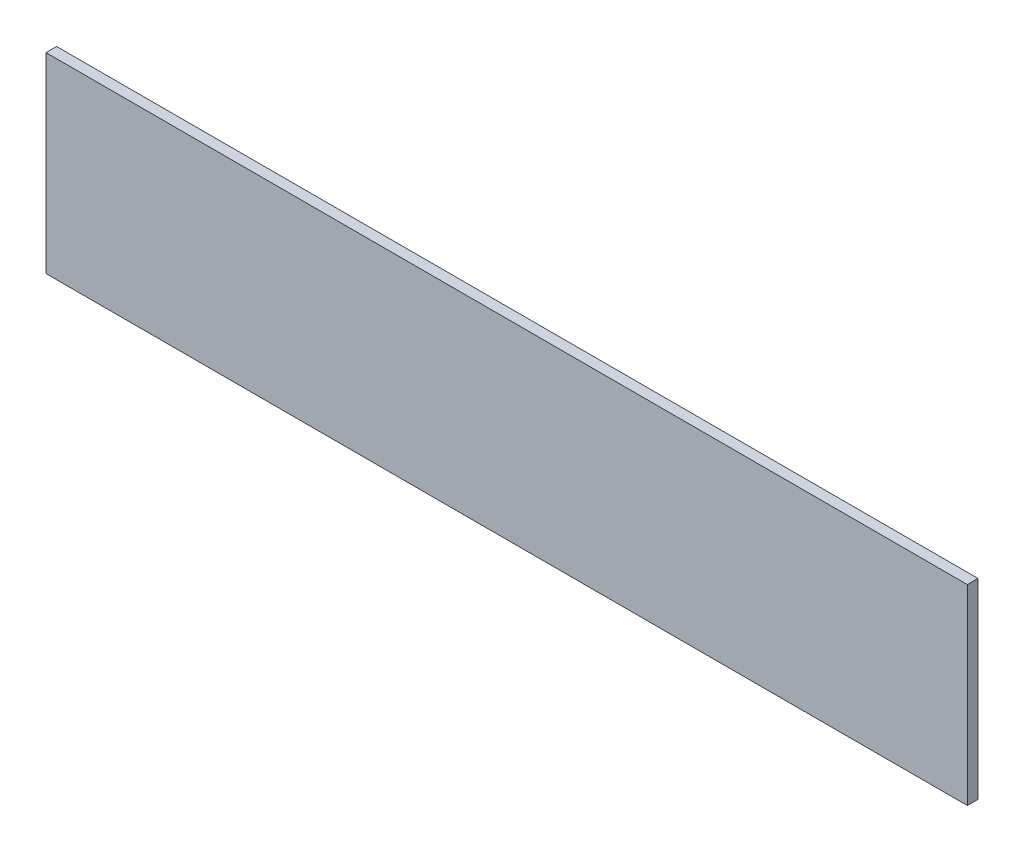
SolidWorks part; units mm, degrees
ref_plane "Plano frontal" through (0, 0, 0) normal (0, 0, 1) x (1, 0, 0)
ref_plane "Plano superior" through (0, 0, 0) normal (0, 1, 0) x (1, 0, 0)
ref_plane "Plano direito" through (0, 0, 0) normal (1, 0, 0) x (0, 0, -1)
sketch "Esboço1" plane through (0, 0, 0) normal (0, 0, 1) x (1, 0, 0)
  line L1 (0, 0) -> (260, 0)
  line L2 (0, 0) -> (0, -54)
  line L3 (0, -54) -> (260, -54)
  line L4 (260, 0) -> (260, -54)
  dimension "D1" = 260
  dimension "D2" = 54
extrude "Ressalto-extrusão1" add sketch "Esboço1" along normal blind 3
